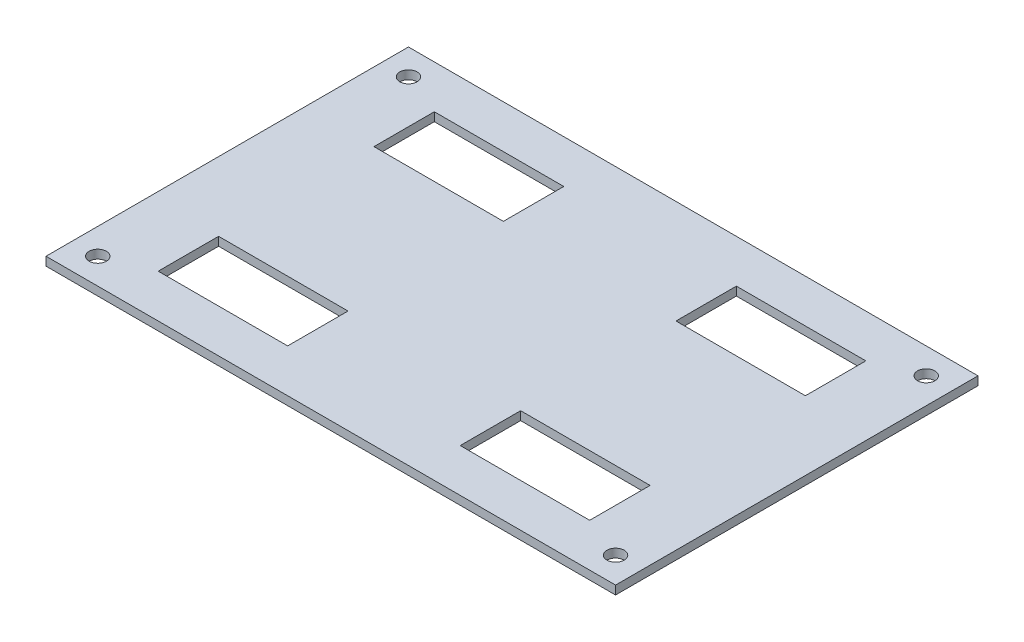
SolidWorks part; units mm, degrees
material "6061-T6 (SS)"
ref_plane "Front Plane" through (0, 0, 0) normal (0, 0, 1) x (1, 0, 0)
ref_plane "Top Plane" through (0, 0, 0) normal (0, 1, 0) x (1, 0, 0)
ref_plane "Right Plane" through (0, 0, 0) normal (1, 0, 0) x (0, 0, -1)
sketch "Sketch1" plane through (0, 0, 0) normal (0, 1, 0) x (1, 0, 0)
  line L1 (-33, -21) -> (33, -21)
  line L2 (-33, -21) -> (-33, 21)
  line L3 (-33, 21) -> (33, 21)
  line L4 (33, -21) -> (33, 21)
  line L5 (-25, -16) -> (-10, -16)
  line L6 (-25, -16) -> (-25, -9)
  line L7 (-25, -9) -> (-10, -9)
  line L8 (-10, -16) -> (-10, -9)
  line L9 (10, -9) -> (25, -9)
  line L10 (10, -9) -> (10, -16)
  line L11 (10, -16) -> (25, -16)
  line L12 (25, -9) -> (25, -16)
  line L13 (10, 16) -> (25, 16)
  line L14 (10, 16) -> (10, 9)
  line L15 (10, 9) -> (25, 9)
  line L16 (25, 16) -> (25, 9)
  line L17 (-10, 9) -> (-25, 9)
  line L18 (-10, 9) -> (-10, 16)
  line L19 (-10, 16) -> (-25, 16)
  line L20 (-25, 9) -> (-25, 16)
  circle A0 centre (-30, -18) radius 1
  circle A1 centre (30, -18) radius 1
  circle A2 centre (30, 18) radius 1
  circle A3 centre (-30, 18) radius 1
  point P13 (-33, 0)
  point P14 (0, -21)
  dimension "D7" = 2
  dimension "D8" = 2
  dimension "D9" = 2
  dimension "D10" = 2
  dimension "D1" = 66
  dimension "D2" = 42
  dimension "D3" = 3
  dimension "D4" = 3
  dimension "D5" = 3
  dimension "D6" = 3
  dimension "D11" = 5
  dimension "D12" = 8
  dimension "D13" = 15
  dimension "D14" = 7
  dimension "D15" = 5
  dimension "D16" = 8
  dimension "D17" = 7
  dimension "D18" = 15
extrude "Boss-Extrude1" add sketch "Sketch1" along normal blind 1
